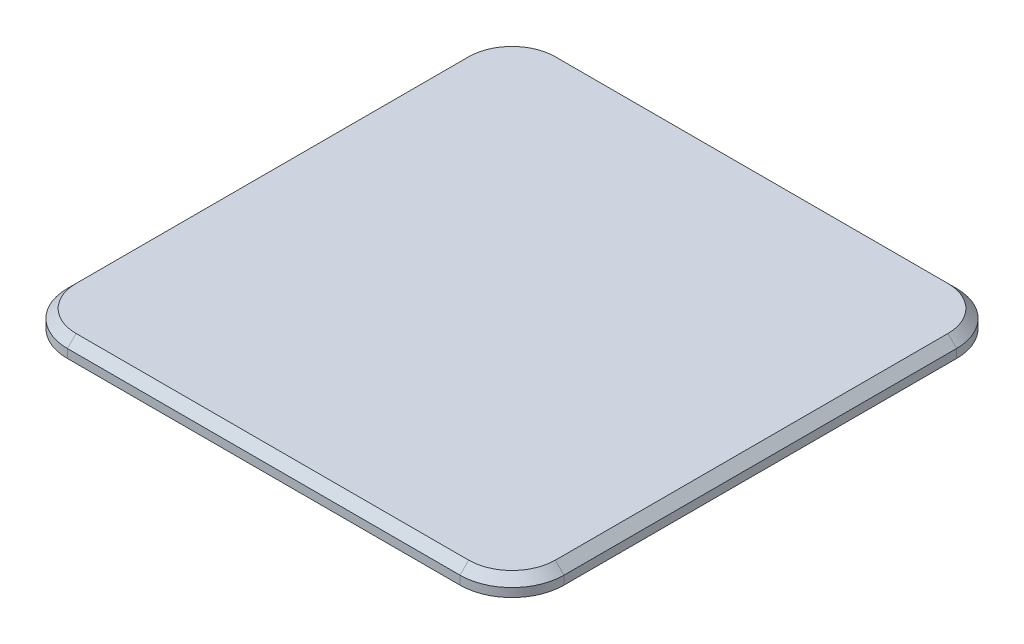
SolidWorks part; units mm, degrees
ref_plane "Front Plane" through (0, 0, 0) normal (0, 0, 1) x (1, 0, 0)
ref_plane "Top Plane" through (0, 0, 0) normal (0, 1, 0) x (1, 0, 0)
ref_plane "Right Plane" through (0, 0, 0) normal (1, 0, 0) x (0, 0, -1)
sketch "Sketch1" plane through (0, 0, 0) normal (0, 1, 0) x (1, 0, 0)
  line L1 (-11.325, 14.325) -> (11.325, 14.325)
  line L2 (-14.325, 11.325) -> (-14.325, -11.325)
  line L3 (-11.325, -14.325) -> (11.325, -14.325)
  line L4 (14.325, 11.325) -> (14.325, -11.325)
  line L5 (-14.325, 14.325) -> (14.325, -14.325) construction
  line L6 (-14.325, -14.325) -> (14.325, 14.325) construction
  arc A0 (-14.325, -11.325) -> (-11.325, -14.325) centre (-11.325, -11.325) ccw
  arc A1 (11.325, -14.325) -> (14.325, -11.325) centre (11.325, -11.325) ccw
  arc A2 (11.325, 14.325) -> (14.325, 11.325) centre (11.325, 11.325) cw
  arc A3 (-11.325, 14.325) -> (-14.325, 11.325) centre (-11.325, 11.325) ccw
  point P0 (0, 0)
  dimension "D3" = 3
  dimension "D1" = 28.65
  dimension "D2" = 28.65
extrude "Boss-Extrude1" add sketch "Sketch1" along normal blind 1
chamfer "Chamfer1" distance 0.5 angle 45 8 edges at (-14.325, 1, 0) (-13.4463, 1, -13.4463) (0, 1, -14.325) (13.4463, 1, -13.4463) (14.325, 1, 0) (13.4463, 1, 13.4463) (0, 1, 14.325) (-13.4463, 1, 13.4463)
